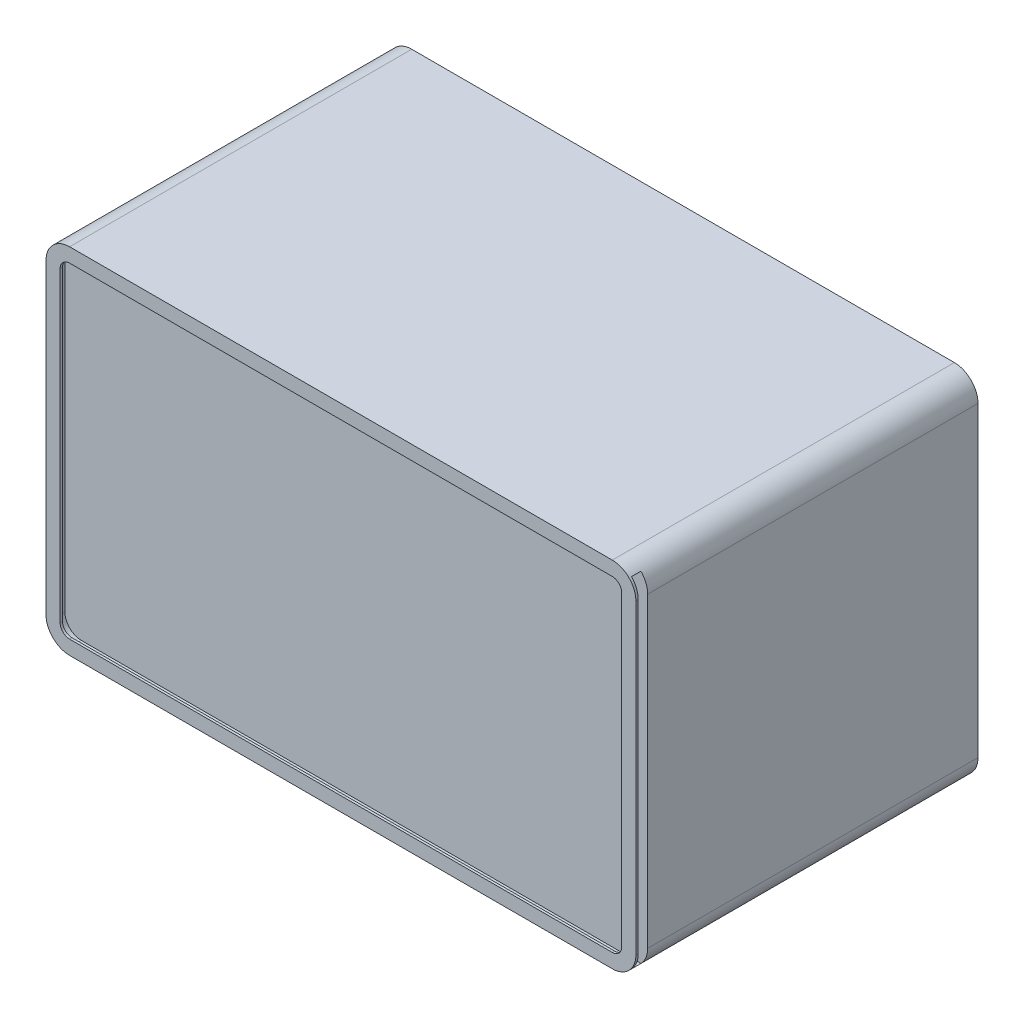
SolidWorks part; units mm, degrees
material "PPE"
ref_plane "Front Plane" through (0, 0, 0) normal (0, 0, 1) x (1, 0, 0)
ref_plane "Top Plane" through (0, 0, 0) normal (0, 1, 0) x (1, 0, 0)
ref_plane "Right Plane" through (0, 0, 0) normal (1, 0, 0) x (0, 0, -1)
sketch "Sketch2" plane through (0, 0, 0) normal (0, 0, 1) x (1, 0, 0)
  line L1 (10, 0) -> (240, 0)
  line L2 (0, 10) -> (0, 140)
  line L3 (10, 150) -> (240, 150)
  line L4 (250, 10) -> (250, 140)
  arc A0 (240, 150) -> (250, 140) centre (240, 140) cw
  arc A1 (240, 0) -> (250, 10) centre (240, 10) ccw
  arc A2 (10, 0) -> (0, 10) centre (10, 10) cw
  arc A3 (0, 140) -> (10, 150) centre (10, 140) cw
  point P11 (0, 0)
  dimension "D1" = 10
  dimension "D2" = 250
  dimension "D3" = 150
extrude "Boss-Extrude1" add sketch "Sketch2" along normal blind 150
shell "Shell2" thickness 3
sketch "Sketch4" plane through (0, 0, 0) normal (0, 0, -1) x (-1, 0, 0)
  line L0 (-10, 3) -> (-240, 3) construction
  line L1 (-3, 140) -> (-3, 10) construction
  line L2 (-240, 147) -> (-10, 147) construction
  line L3 (-247, 10) -> (-247, 140) construction
  line L4 (-10, 3) -> (-240, 3)
  line L5 (-3, 140) -> (-3, 10)
  line L6 (-240, 147) -> (-10, 147)
  line L7 (-247, 10) -> (-247, 140)
  arc A0 (-10, 3) -> (-3, 10) centre (-10, 10) ccw construction
  arc A1 (-247, 10) -> (-240, 3) centre (-240, 10) ccw construction
  arc A2 (-3, 140) -> (-10, 147) centre (-10, 140) ccw construction
  arc A3 (-240, 147) -> (-247, 140) centre (-240, 140) ccw construction
  arc A4 (-10, 3) -> (-3, 10) centre (-10, 10) ccw
  arc A5 (-247, 10) -> (-240, 3) centre (-240, 10) ccw
  arc A6 (-3, 140) -> (-10, 147) centre (-10, 140) ccw
  arc A7 (-240, 147) -> (-247, 140) centre (-240, 140) ccw
extrude "Boss-Extrude2" add sketch "Sketch4" against normal blind 3
sketch "Sketch5" plane through (0, 0, 150) normal (0, 0, 1) x (1, 0, 0)
  line L5 (240, 150) -> (10, 150)
  line L6 (0, 140) -> (0, 10)
  line L7 (10, 0) -> (240, 0)
  line L8 (250, 10) -> (250, 140)
  line L9 (240, 150) -> (10, 150)
  line L10 (0, 140) -> (0, 10)
  line L11 (10, 0) -> (240, 0)
  line L12 (250, 10) -> (250, 140)
  arc A4 (250, 140) -> (240, 150) centre (240, 140) ccw
  arc A5 (10, 150) -> (0, 140) centre (10, 140) ccw
  arc A6 (0, 10) -> (10, 0) centre (10, 10) ccw
  arc A7 (240, 0) -> (250, 10) centre (240, 10) ccw
  arc A8 (250, 140) -> (240, 150) centre (240, 140) ccw
  arc A9 (10, 150) -> (0, 140) centre (10, 140) ccw
  arc A10 (0, 10) -> (10, 0) centre (10, 10) ccw
  arc A11 (240, 0) -> (250, 10) centre (240, 10) ccw
  dimension "D1" = 0
extrude "Cut-Extrude1" cut sketch "Sketch5" against normal blind 5
ref_plane "Plane2" through (0, 0, 135) normal (0, 0, 1) x (1, 0, 0)
sketch "Sketch6" plane through (0, 0, 135) normal (0, 0, 1) x (1, 0, 0)
  line L0 (10, 3) -> (240, 3) construction
  line L1 (247, 10) -> (247, 140) construction
  line L2 (240, 147) -> (10, 147) construction
  line L3 (3, 140) -> (3, 10) construction
  line L4 (10, 3) -> (240, 3)
  line L5 (247, 10) -> (247, 140)
  line L6 (240, 147) -> (10, 147)
  line L7 (3, 140) -> (3, 10)
  arc A0 (3, 10) -> (10, 3) centre (10, 10) ccw construction
  arc A1 (240, 3) -> (247, 10) centre (240, 10) ccw construction
  arc A2 (247, 140) -> (240, 147) centre (240, 140) ccw construction
  arc A3 (10, 147) -> (3, 140) centre (10, 140) ccw construction
  arc A4 (3, 10) -> (10, 3) centre (10, 10) ccw
  arc A5 (240, 3) -> (247, 10) centre (240, 10) ccw
  arc A6 (247, 140) -> (240, 147) centre (240, 140) ccw
  arc A7 (10, 147) -> (3, 140) centre (10, 140) ccw
extrude "Boss-Extrude3" add sketch "Sketch6" along normal blind 5
ref_plane "Plane3" through (0, 0, 144) normal (0, 0, 1) x (1, 0, 0)
sketch "Sketch7" plane through (0, 0, 144) normal (0, 0, 1) x (1, 0, 0)
  line L0 (10, 3) -> (240, 3) construction
  line L1 (247, 10) -> (247, 140) construction
  line L2 (240, 147) -> (10, 147) construction
  line L3 (3, 140) -> (3, 10) construction
  line L4 (10, 3) -> (240, 3)
  line L5 (247, 10) -> (247, 140)
  line L6 (240, 147) -> (10, 147)
  line L7 (3, 140) -> (3, 10)
  line L8 (6, 140) -> (6, 10)
  line L9 (10, 6) -> (240, 6)
  line L10 (244, 10) -> (244, 140)
  line L11 (240, 144) -> (10, 144)
  arc A0 (3, 10) -> (10, 3) centre (10, 10) ccw construction
  arc A1 (240, 3) -> (247, 10) centre (240, 10) ccw construction
  arc A2 (247, 140) -> (240, 147) centre (240, 140) ccw construction
  arc A3 (3, 10) -> (10, 3) centre (10, 10) ccw
  arc A4 (240, 3) -> (247, 10) centre (240, 10) ccw
  arc A5 (247, 140) -> (240, 147) centre (240, 140) ccw
  arc A6 (10, 147) -> (3, 140) centre (10, 140) ccw construction
  arc A7 (10, 147) -> (3, 140) centre (10, 140) ccw
  arc A8 (6, 10) -> (10, 6) centre (10, 10) ccw
  arc A9 (240, 6) -> (244, 10) centre (240, 10) ccw
  arc A10 (244, 140) -> (240, 144) centre (240, 140) ccw
  arc A11 (10, 144) -> (6, 140) centre (10, 140) ccw
  dimension "D1" = 3
extrude "Boss-Extrude4" add sketch "Sketch7" along normal up to vertex (4 mm away) from offset 0
sketch "Sketch10" plane through (250, 0, 0) normal (1, 0, 0) x (0, 0, -1)
  line L0 (-145, 150) -> (0, 150) construction
  line L1 (-144, 147) -> (-139, 147)
  line L2 (-144, 147) -> (-144, 3)
  line L3 (-144, 3) -> (-139, 3)
  line L4 (-139, 147) -> (-139, 3)
  line L5 (-145, 0) -> (0, 0) construction
  line L7 (-145, 10) -> (-145, 140) construction
  point P8 (-130.4341, 3)
  dimension "D1" = 3
  dimension "D2" = 3
  dimension "D3" = 5
  dimension "D4" = 1
extrude "Cut-Extrude2" cut sketch "Sketch10" against normal blind 8
sketch "Sketch11" plane through (242, 0, 0) normal (1, 0, 0) x (0, 0, -1)
  line L0 (-139, 3) -> (-139, 147) construction
  line L1 (-144, 3) -> (-139, 3)
  line L2 (-144, 3) -> (-144, 147)
  line L3 (-144, 147) -> (-139, 147)
  line L4 (-139, 3) -> (-139, 147)
  point P5 (-139, 83.9833)
  point P8 (-139, 147)
extrude "Cut-Extrude3" cut sketch "Sketch11" against normal blind 8
sketch "Sketch12" plane through (234, 0, 0) normal (1, 0, 0) x (0, 0, -1)
  line L4 (-140, 147) -> (-140, 3)
  line L5 (-140, 3) -> (-139, 3)
  line L6 (-139, 3) -> (-139, 147)
  line L7 (-139, 147) -> (-140, 147)
  line L8 (-140, 147) -> (-140, 3)
  line L9 (-140, 3) -> (-139, 3)
  line L10 (-139, 3) -> (-139, 147)
  line L11 (-139, 147) -> (-140, 147)
  dimension "D1" = 0
extrude "Boss-Extrude5" add sketch "Sketch12" along normal up to surface (16 mm away) up to face at (250, 75, 69.5)
sketch "Sketch13" plane through (0, 0, 139) normal (0, 0, -1) x (-1, 0, 0)
  line L2 (-250, 3) -> (-247.1414, 3)
  line L3 (-250, 10) -> (-250, 3)
  line L4 (-250, 3) -> (-247.1414, 3)
  line L5 (-250, 10) -> (-250, 3)
  arc A1 (-250, 10) -> (-247.1414, 3) centre (-240, 10) ccw
  arc A2 (-250, 10) -> (-247.1414, 3) centre (-240, 10) ccw
  dimension "D1" = 0
extrude "Cut-Extrude4" cut sketch "Sketch13" against normal blind 8
sketch "Sketch14" plane through (0, 0, 139) normal (0, 0, -1) x (-1, 0, 0)
  line L2 (-250, 147) -> (-250, 140)
  line L3 (-247.1414, 147) -> (-250, 147)
  line L4 (-250, 147) -> (-250, 140)
  line L5 (-247.1414, 147) -> (-250, 147)
  arc A1 (-247.1414, 147) -> (-250, 140) centre (-240, 140) ccw
  arc A2 (-247.1414, 147) -> (-250, 140) centre (-240, 140) ccw
  dimension "D1" = 0
extrude "Cut-Extrude5" cut sketch "Sketch14" against normal blind 8
sketch "Sketch15" plane through (0, 0, 0) normal (0, -1, 0) x (1, 0, 0)
  line L0 (125, 145) -> (125, 102.0921) construction
  line L2 (10, 0) -> (240, 0) construction
  line L5 (10, 145) -> (240, 145) construction
  circle A0 centre (102.5, 97.5) radius 4
  circle A1 centre (102.5, 47.5) radius 4
  circle A2 centre (147.5, 47.5) radius 4
  circle A3 centre (147.5, 97.5) radius 4
  point P0 (7, 72.5)
  point P13 (0, 0)
  dimension "D5" = 8
  dimension "D1" = 8
  dimension "D2" = 50
  dimension "D6" = 47.5
  dimension "D3" = 47.5
  dimension "D4" = 22.5
extrude "Cut-Extrude13" cut sketch "Sketch15" against normal blind 9
